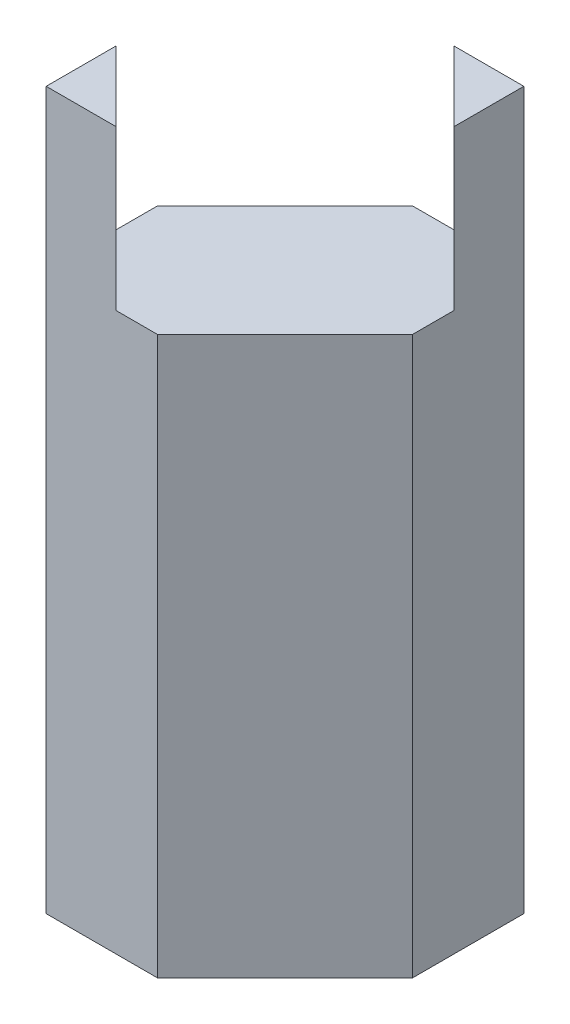
SolidWorks part; units mm, degrees
material "ABS"
ref_plane "Front Plane" through (0, 0, 0) normal (0, 0, 1) x (1, 0, 0)
ref_plane "Top Plane" through (0, 0, 0) normal (0, 1, 0) x (1, 0, 0)
ref_plane "Right Plane" through (0, 0, 0) normal (1, 0, 0) x (0, 0, -1)
sketch "Sketch1" plane through (0, 0, 0) normal (0, 1, 0) x (1, 0, 0)
  line L1 (-9.525, -9.525) -> (9.525, -9.525)
  line L2 (-9.525, -9.525) -> (-9.525, 9.525)
  line L3 (-9.525, 9.525) -> (9.525, 9.525)
  line L4 (9.525, -9.525) -> (9.525, 9.525)
  line L5 (-9.525, -9.525) -> (9.525, 9.525) construction
  line L6 (-9.525, 9.525) -> (9.525, -9.525) construction
  point P0 (0, 0)
extrude "Boss-Extrude1" add sketch "Sketch1" along normal blind 44.45
sketch "Sketch2" plane through (0, 44.45, 0) normal (0, 1, 0) x (1, 0, 0)
  line L5 (-9.525, -9.525) -> (-3.9572, -9.525)
  line L6 (-9.525, -9.525) -> (9.525, -9.525) construction
  line L7 (-3.9572, -9.525) -> (-9.525, -3.9572)
  line L8 (-9.525, 9.525) -> (-9.525, -9.525) construction
  line L9 (-9.525, -3.9572) -> (-9.525, -9.525)
  dimension "D1" = 3.937
extrude "Boss-Extrude2" add sketch "Sketch2" along normal blind 12.7
ref_plane "Plane1" through (0, 0, 0) normal (-0.7071, 0, 0.7071) x (0.7071, 0, 0.7071)
mirror "Mirror1" about plane through (0, 0, 0) normal (-0.7071, 0, 0.7071) of "Boss-Extrude2"
sketch "Sketch3" plane through (0, 44.45, 0) normal (0, 1, 0) x (1, 0, 0)
  line L0 (9.525, -9.525) -> (-0.635, -9.525)
  line L1 (-3.9572, -9.525) -> (9.525, -9.525) construction
  line L2 (-0.635, -9.525) -> (9.525, 0.635)
  line L3 (9.525, -9.525) -> (9.525, 3.9572) construction
  line L4 (9.525, 0.635) -> (9.525, -9.525)
ref_plane "Plane2" through (0, 0, 0) normal (-0.7071, 0, -0.7071) x (-0.7071, 0, 0.7071)
extrude "Cut-Extrude1" cut sketch "Sketch3" against normal through all
mirror "Mirror2" about plane through (0, 0, 0) normal (-0.7071, 0, -0.7071) of "Cut-Extrude1"
